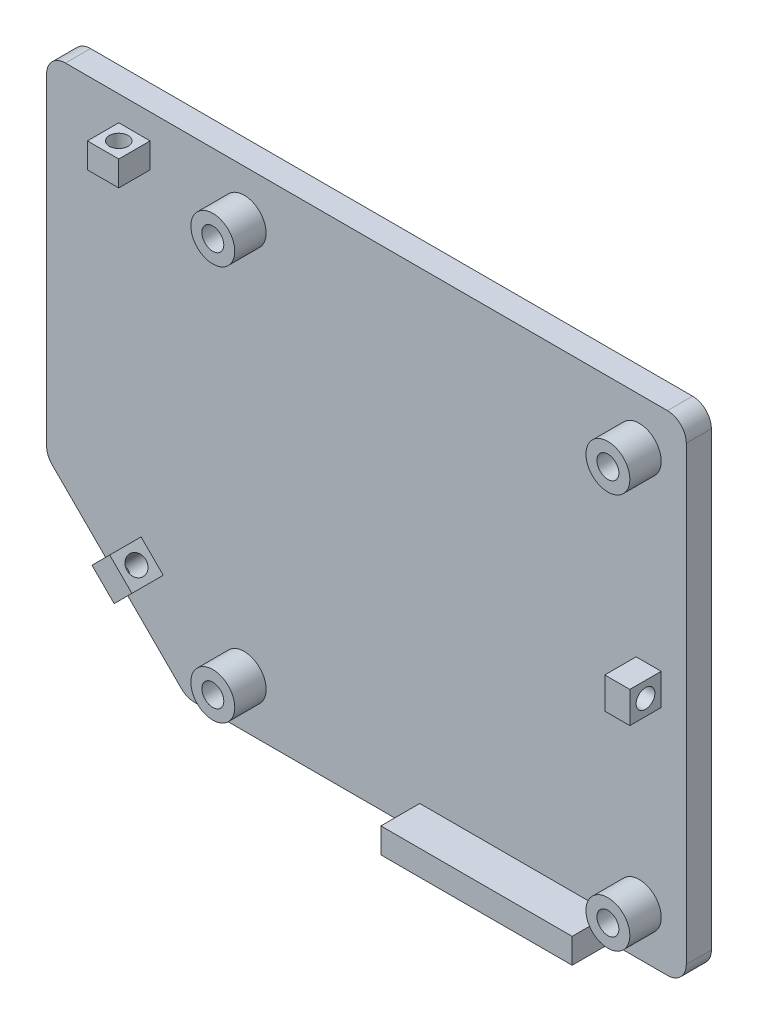
SolidWorks part; units mm, degrees
ref_plane "Alzado" through (0, 0, 0) normal (0, 0, 1) x (1, 0, 0)
ref_plane "Planta" through (0, 0, 0) normal (0, 1, 0) x (1, 0, 0)
ref_plane "Vista lateral" through (0, 0, 0) normal (1, 0, 0) x (0, 0, -1)
sketch "Croquis1" plane through (0, 0, 0) normal (0, 0, 1) x (1, 0, 0)
  line L1 (0, 0) -> (102, 0)
  line L2 (0, 0) -> (0, 78)
  line L3 (0, 78) -> (102, 78)
  line L4 (102, 0) -> (102, 78)
  dimension "D1" = 78
  dimension "D2" = 102
extrude "Saliente-Extruir1" add sketch "Croquis1" along normal blind 4
sketch "Croquis2" plane through (0, 0, 4) normal (0, 0, 1) x (1, 0, 0)
  line L0 (102, 78) -> (0, 78) construction
  line L1 (98, 74) -> (28, 74) construction
  line L2 (98, 74) -> (98, 4) construction
  line L3 (98, 4) -> (28, 4) construction
  line L4 (28, 74) -> (28, 4) construction
  line L5 (0, 0) -> (102, 0) construction
  line L6 (102, 0) -> (102, 78) construction
  line L7 (94.5, 70.5) -> (31.5, 70.5) construction
  line L8 (31.5, 70.5) -> (31.5, 7.5) construction
  line L9 (94.5, 7.5) -> (31.5, 7.5) construction
  line L10 (94.5, 70.5) -> (94.5, 7.5) construction
  circle A0 centre (94.5, 70.5) radius 1.75
  circle A1 centre (31.5, 70.5) radius 1.75
  circle A2 centre (31.5, 7.5) radius 1.75
  circle A3 centre (94.5, 7.5) radius 1.75
  dimension "D6" = 3.5
  dimension "D7" = 3.5
  dimension "D8" = 3.5
  dimension "D9" = 3.5
  dimension "D1" = 4
  dimension "D2" = 4
  dimension "D3" = 4
  dimension "D4" = 70
  dimension "D5" = 3.5
extrude "Cortar-Extruir1" cut sketch "Croquis2" against normal blind 4
sketch "Croquis3" plane through (0, 0, 4) normal (0, 0, 1) x (1, 0, 0)
  line L9 (0, 4) -> (98, 4)
  line L10 (98, 4) -> (98, 74)
  line L11 (98, 74) -> (0, 74)
  line L12 (0, 4) -> (98, 4) construction
  line L13 (98, 4) -> (98, 74) construction
  line L14 (98, 74) -> (0, 74) construction
  circle A0 centre (31.5, 70.5) radius 3.5
  circle A1 centre (31.5, 70.5) radius 1.75
  circle A2 centre (94.5, 70.5) radius 3.5
  circle A3 centre (94.5, 70.5) radius 1.75
  circle A4 centre (31.5, 7.5) radius 3.5
  circle A5 centre (31.5, 7.5) radius 1.75
  circle A6 centre (94.5, 7.5) radius 3.5
  circle A7 centre (94.5, 7.5) radius 1.75
  dimension "D1" = 4
extrude "Saliente-Extruir2" add sketch "Croquis3" along normal blind 5
sketch "Croquis4" plane through (0, 0, 4) normal (0, 0, 1) x (1, 0, 0)
  line L6 (0, 0) -> (102, 0) construction
  line L7 (59.5, 0) -> (90, 0)
  line L8 (59.5, 0) -> (59.5, 4)
  line L9 (0, 4) -> (98, 4)
  line L10 (98, 4) -> (98, 74)
  line L11 (98, 74) -> (0, 74)
  line L12 (0, 4) -> (98, 4) construction
  line L13 (98, 4) -> (98, 74) construction
  line L14 (98, 74) -> (0, 74) construction
  line L15 (59.5, 4) -> (90, 4)
  line L16 (90, 0) -> (90, 4)
  dimension "D2" = 30.5
  dimension "D3" = 8
  dimension "D1" = 4
extrude "Saliente-Extruir3" add sketch "Croquis4" along normal blind 6.2
sketch "Croquis5" plane through (0, 0, 4) normal (0, 0, 1) x (1, 0, 0)
  line L1 (4, 70) -> (14, 70) construction
  line L11 (14, 70) -> (11.5, 70)
  line L13 (14, 74) -> (11.5, 74)
  line L14 (11.5, 70) -> (11.5, 74)
  line L15 (14, 70) -> (16.5, 70)
  line L17 (98, 39) -> (98, 41.5)
  line L18 (98, 41.5) -> (94, 41.5)
  line L19 (94, 39) -> (94, 41.5)
  line L20 (90, 4) -> (98, 4)
  line L21 (59.5, 4) -> (90, 4)
  line L22 (0, 4) -> (59.5, 4)
  line L23 (98, 4) -> (98, 74)
  line L24 (98, 74) -> (0, 74)
  line L25 (90, 4) -> (98, 4) construction
  line L26 (59.5, 4) -> (90, 4) construction
  line L28 (98, 4) -> (98, 74) construction
  line L29 (98, 74) -> (0, 74) construction
  line L31 (98, 39) -> (98, 36.5)
  line L32 (98, 36.5) -> (94, 36.5)
  line L33 (94, 39) -> (94, 36.5)
  line L35 (4, 78) -> (4, 0)
  line L36 (4, 78) -> (4, 0) construction
  line L37 (14, 74) -> (16.5, 74)
  line L38 (16.5, 70) -> (16.5, 74)
  dimension "D2" = 4
  dimension "D3" = 2.5
  dimension "D4" = 2.5
  dimension "D10" = 10
  dimension "D11" = 4
  dimension "D1" = 4
  dimension "D5" = 4
extrude "Saliente-Extruir4" add sketch "Croquis5" along normal blind 5
sketch "Croquis7" plane through (98, 0, 0) normal (1, 0, 0) x (0, 0, -1)
  line L0 (-9, 36.5) -> (-4, 41.5) construction
  circle A0 centre (-6.5, 39) radius 1.5
extrude "Cortar-Extruir3" cut sketch "Croquis7" against normal blind 5
sketch "Croquis8" plane through (0, 0, 4) normal (0, 0, 1) x (1, 0, 0)
  line L0 (0, 0) -> (22.34, 0)
  line L1 (0, 0) -> (59.5, 0) construction
  line L2 (22.34, 0) -> (0, 22.34)
  line L3 (0, 78) -> (0, 0) construction
  line L4 (0, 22.34) -> (0, 0)
  dimension "D1" = 22.34
extrude "Cortar-Extruir5" cut sketch "Croquis8" against normal through all both and the other way through all
sketch "Croquis11" plane through (0, 74, 0) normal (0, 1, 0) x (1, 0, 0)
  line L0 (16.5, -9) -> (11.5, -4) construction
  circle A0 centre (14, -6.5) radius 1.5
  dimension "D1" = 3
extrude "Cortar-Extruir6" cut sketch "Croquis11" against normal up to surface (4 mm away) up to face at (14, 70, 6.5)
sketch "Croquis12" plane through (0, 0, 4) normal (0, 0, 1) x (1, 0, 0)
  line L10 (13.9984, 13.9984) -> (15.7662, 12.2307)
  line L11 (2.8284, 25.1684) -> (25.1684, 2.8284)
  line L12 (2.8284, 25.1684) -> (25.1684, 2.8284) construction
  line L13 (15.7662, 12.2307) -> (18.5946, 15.0591)
  line L14 (18.5946, 15.0591) -> (15.0591, 18.5946)
  line L15 (15.0591, 18.5946) -> (12.2307, 15.7662)
  line L16 (12.2307, 15.7662) -> (13.9984, 13.9984)
  dimension "D2" = 5
  dimension "D3" = 2.5
  dimension "D4" = 4
  dimension "D1" = 4
extrude "Saliente-Extruir5" add sketch "Croquis12" along normal blind 5
sketch "Croquis13" plane through (13.9984, 13.9984, 0) normal (-0.7071, -0.7071, 0) x (0, 0, 1)
  line L0 (9, 2.5) -> (4, -2.5) construction
  circle A0 centre (6.5, 0) radius 1.5
  dimension "D1" = 3
extrude "Cortar-Extruir7" cut sketch "Croquis13" against normal blind 5
fillet "Redondeo1" radius 3 5 edges at (102, 78, 2) (102, 0, 2) (22.34, 0, 2) (0, 22.34, 2) (0, 78, 2)
